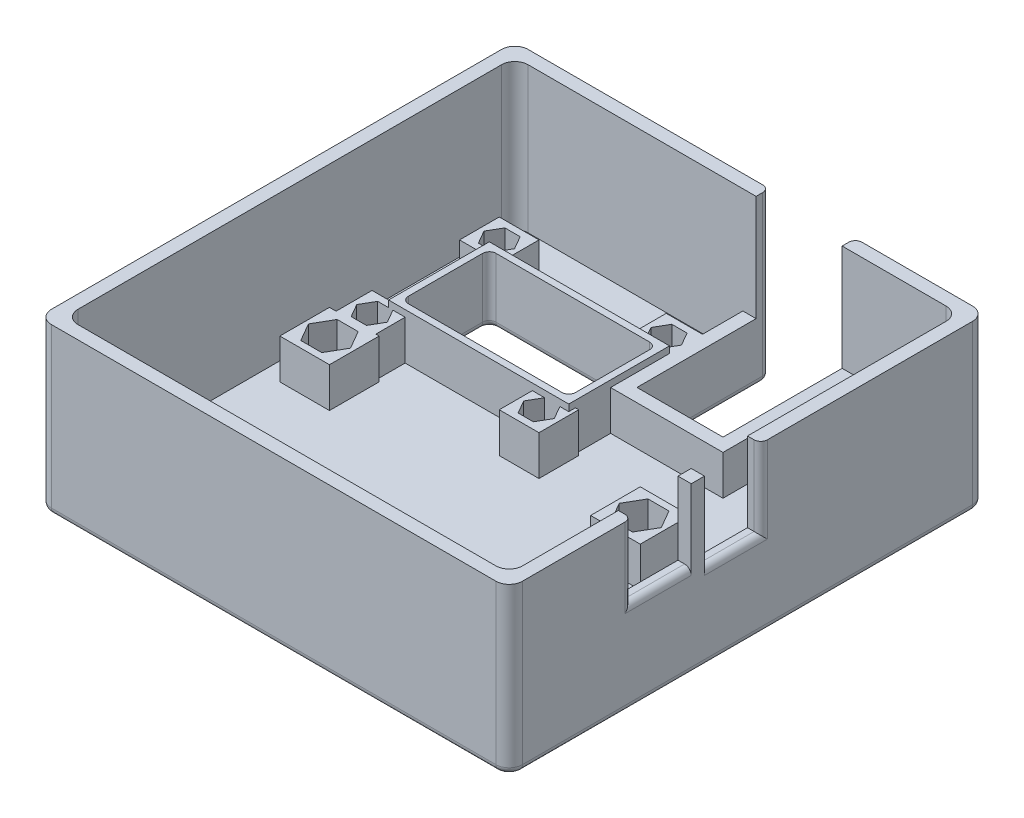
SolidWorks part; units mm, degrees
material "ABS"
ref_plane "Plano frontal" through (0, 0, 0) normal (0, 0, 1) x (1, 0, 0)
ref_plane "Plano superior" through (0, 0, 0) normal (0, 1, 0) x (1, 0, 0)
ref_plane "Plano direito" through (0, 0, 0) normal (1, 0, 0) x (0, 0, -1)
sketch "Esboço1" plane through (0, 0, 0) normal (0, 1, 0) x (1, 0, 0)
  line L1 (35.575, -36) -> (-35.575, -36)
  line L2 (35.575, -36) -> (35.575, 36)
  line L3 (35.575, 36) -> (-35.575, 36)
  line L4 (-35.575, -36) -> (-35.575, 36)
  line L5 (35.575, -36) -> (-35.575, 36) construction
  line L6 (35.575, 36) -> (-35.575, -36) construction
  point P0 (0, 0)
  dimension "D1" = 71.15
  dimension "D2" = 72
extrude "Ressalto-extrusão1" add sketch "Esboço1" along normal mid plane 3
sketch "Esboço2" plane through (0, 1.5, 0) normal (0, 1, 0) x (1, 0, 0)
  line L8 (-33.575, 34) -> (-33.575, -34)
  line L9 (-33.575, -34) -> (33.575, -34)
  line L10 (33.575, -34) -> (33.575, 34)
  line L11 (33.575, 34) -> (-33.575, 34)
  line L12 (-33.575, 34) -> (-33.575, -34)
  line L13 (-33.575, -34) -> (33.575, -34)
  line L14 (33.575, -34) -> (33.575, 34)
  line L15 (33.575, 34) -> (-33.575, 34)
  line L16 (-35.575, 36) -> (-35.575, -36)
  line L17 (-35.575, -36) -> (35.575, -36)
  line L18 (35.575, -36) -> (35.575, 36)
  line L19 (35.575, 36) -> (-35.575, 36)
  line L20 (-35.575, 36) -> (-35.575, -36)
  line L21 (-35.575, -36) -> (35.575, -36)
  line L22 (35.575, -36) -> (35.575, 36)
  line L23 (35.575, 36) -> (-35.575, 36)
  dimension "D1" = 2
  dimension "D2" = 0
extrude "Ressalto-extrusão2" add sketch "Esboço2" along normal blind 22
fillet "Filete1" radius 2 8 edges at (33.575, 12.5, -34) (35.575, 11, -36) (33.575, 12.5, 34) (35.575, 11, 36) (-33.575, 12.5, 34) (-35.575, 11, 36) (-35.575, 11, -36) (-33.575, 12.5, -34)
sketch "Esboço3" plane through (0, 0, -36) normal (0, 0, -1) x (-1, 0, 0)
  line L0 (-33.575, 23.5) -> (33.575, 23.5) construction
  line L1 (-15.875, 23.5) -> (-2.875, 23.5)
  line L2 (-15.875, 23.5) -> (-15.875, -1.5)
  line L3 (-15.875, -1.5) -> (-2.875, -1.5)
  line L4 (-2.875, 23.5) -> (-2.875, -1.5)
  line L6 (-33.575, -1.5) -> (33.575, -1.5) construction
  line L7 (-33.575, 23.5) -> (-33.575, -1.5) construction
  dimension "D1" = 17.7
  dimension "D2" = 13
extrude "Corte-extrusão1" cut sketch "Esboço3" against normal blind 20
sketch "Esboço4" plane through (0, 1.5, 0) normal (0, 1, 0) x (1, 0, 0)
  line L0 (17.875, 34) -> (17.875, 14)
  line L1 (17.875, 14) -> (0.875, 14)
  line L2 (0.875, 14) -> (0.875, 34)
  line L8 (15.875, 34) -> (15.875, 16)
  line L9 (15.875, 16) -> (2.875, 16)
  line L10 (2.875, 16) -> (2.875, 34)
  line L11 (2.875, 34) -> (-31.575, 34)
  line L12 (-33.575, 32) -> (-33.575, -32)
  line L13 (-31.575, -34) -> (31.575, -34)
  line L14 (33.575, -32) -> (33.575, 32)
  line L15 (31.575, 34) -> (15.875, 34)
  line L16 (15.875, 34) -> (15.875, 16)
  line L17 (15.875, 16) -> (2.875, 16)
  line L18 (2.875, 16) -> (2.875, 34)
  line L19 (2.875, 34) -> (0.875, 34)
  line L23 (17.875, 34) -> (15.875, 34)
  arc A4 (-31.575, 34) -> (-33.575, 32) centre (-31.575, 32) ccw
  arc A5 (-33.575, -32) -> (-31.575, -34) centre (-31.575, -32) ccw
  arc A6 (31.575, -34) -> (33.575, -32) centre (31.575, -32) ccw
  arc A7 (33.575, 32) -> (31.575, 34) centre (31.575, 32) ccw
  dimension "D1" = 0
  dimension "D2" = 2
extrude "Ressalto-extrusão3" add sketch "Esboço4" along normal blind 6
sketch "Esboço5" plane through (35.575, 0, 0) normal (1, 0, 0) x (0, 0, -1)
  line L0 (-34, 23.5) -> (34, 23.5) construction
  line L1 (-17.5, 23.5) -> (-8.5, 23.5)
  line L2 (-17.5, 23.5) -> (-17.5, 12.5)
  line L3 (-17.5, 12.5) -> (-8.5, 12.5)
  line L4 (-8.5, 23.5) -> (-8.5, 12.5)
  line L6 (-34, 23.5) -> (-34, -1.5) construction
  dimension "D1" = 16.5
  dimension "D2" = 9
  dimension "D3" = 11
extrude "Corte-extrusão2" cut sketch "Esboço5" against normal up to surface (2 mm away) and the other way through all up to face at (33.575, 12.5, 0)
sketch "Esboço6" plane through (35.575, 0, 0) normal (1, 0, 0) x (0, 0, -1)
  line L0 (-8.5, 23.5) -> (34, 23.5) construction
  line L1 (-6.5, 23.5) -> (2, 23.5)
  line L2 (-6.5, 23.5) -> (-6.5, 11.5)
  line L3 (-6.5, 11.5) -> (2, 11.5)
  line L4 (2, 23.5) -> (2, 11.5)
  line L5 (-34, 23.5) -> (-34, -1.5) construction
  dimension "D1" = 27.5
  dimension "D2" = 8.5
  dimension "D3" = 12
extrude "Corte-extrusão3" cut sketch "Esboço6" against normal up to surface (2 mm away) up to face at (33.575, 15.25, 6.5)
sketch "Esboço7" plane through (0, 1.5, 0) normal (0, 1, 0) x (1, 0, 0)
  line L0 (-31.575, -34) -> (31.575, -34) construction
  line L1 (-28.6627, -22.25) -> (-30.2504, -25)
  line L2 (-30.2504, -25) -> (-28.6627, -27.75)
  line L3 (-28.6627, -27.75) -> (-25.4873, -27.75)
  line L4 (-25.4873, -27.75) -> (-23.8996, -25)
  line L5 (-23.8996, -25) -> (-25.4873, -22.25)
  line L6 (-25.4873, -22.25) -> (-28.6627, -22.25)
  line L7 (-33.575, 32) -> (-33.575, -32) construction
  line L8 (-45.3985, -12.75) -> (20.9653, -12.75) construction
  line L9 (-23.325, -28.75) -> (-30.825, -28.75)
  line L10 (-23.325, -28.75) -> (-23.325, -21.25)
  line L11 (-23.325, -21.25) -> (-30.825, -21.25)
  line L12 (-30.825, -28.75) -> (-30.825, -21.25)
  line L13 (-23.325, -28.75) -> (-30.825, -21.25) construction
  line L14 (-23.325, -21.25) -> (-30.825, -28.75) construction
  line L15 (18.2873, -22.25) -> (16.6996, -25)
  line L16 (16.6996, -25) -> (18.2873, -27.75)
  line L17 (18.2873, -27.75) -> (21.4627, -27.75)
  line L18 (21.4627, -27.75) -> (23.0504, -25)
  line L19 (23.0504, -25) -> (21.4627, -22.25)
  line L20 (21.4627, -22.25) -> (18.2873, -22.25)
  line L21 (23.625, -28.75) -> (16.125, -28.75)
  line L22 (23.625, -28.75) -> (23.625, -21.25)
  line L23 (23.625, -21.25) -> (16.125, -21.25)
  line L24 (16.125, -28.75) -> (16.125, -21.25)
  line L25 (23.625, -28.75) -> (16.125, -21.25) construction
  line L26 (23.625, -21.25) -> (16.125, -28.75) construction
  line L27 (23.625, -4.25) -> (16.125, 3.25) construction
  line L28 (23.625, 3.25) -> (16.125, -4.25) construction
  line L29 (-23.325, -4.25) -> (-30.825, 3.25) construction
  line L30 (-23.325, 3.25) -> (-30.825, -4.25) construction
  line L31 (16.125, 3.25) -> (16.125, -4.25)
  line L32 (23.625, -4.25) -> (16.125, -4.25)
  line L33 (23.625, 3.25) -> (23.625, -4.25)
  line L34 (23.625, 3.25) -> (16.125, 3.25)
  line L35 (21.4627, -3.25) -> (18.2873, -3.25)
  line L36 (23.0504, -0.5) -> (21.4627, -3.25)
  line L37 (21.4627, 2.25) -> (23.0504, -0.5)
  line L38 (18.2873, 2.25) -> (21.4627, 2.25)
  line L39 (16.6996, -0.5) -> (18.2873, 2.25)
  line L40 (18.2873, -3.25) -> (16.6996, -0.5)
  line L41 (-30.825, 3.25) -> (-30.825, -4.25)
  line L42 (-23.325, -4.25) -> (-30.825, -4.25)
  line L43 (-23.325, 3.25) -> (-23.325, -4.25)
  line L44 (-23.325, 3.25) -> (-30.825, 3.25)
  line L45 (-25.4873, -3.25) -> (-28.6627, -3.25)
  line L46 (-23.8996, -0.5) -> (-25.4873, -3.25)
  line L47 (-25.4873, 2.25) -> (-23.8996, -0.5)
  line L48 (-28.6627, 2.25) -> (-25.4873, 2.25)
  line L49 (-30.2504, -0.5) -> (-28.6627, 2.25)
  line L50 (-28.6627, -3.25) -> (-30.2504, -0.5)
  circle A0 centre (-27.075, -25) radius 2.75 construction
  circle A1 centre (19.875, -25) radius 2.75 construction
  circle A2 centre (19.875, -0.5) radius 2.75 construction
  circle A3 centre (-27.075, -0.5) radius 2.75 construction
  dimension "D1" = 5.5
  dimension "D2" = 9
  dimension "D3" = 6.5
  dimension "D4" = 1
  dimension "D5" = 5.5
  dimension "D6" = 1
  dimension "D7" = 9
  dimension "D8" = 46.95
  dimension "D9" = 12.25
extrude "Ressalto-extrusão4" add sketch "Esboço7" along normal blind 6 contours L10 L9 L12 L11 | L1 L2 L3 L4 L5 L6 | L22 L21 L24 L23 | L15 L16 L17 L18 L19 L20 | L41 L42 L43 L44 | L45 L50 L49 L48 L47 L46 | L31 L32 L33 L34 | L35 L40 L39 L38 L37 L36
sketch "Esboço8" plane through (0, 1.5, 0) normal (0, 1, 0) x (1, 0, 0)
  line L0 (2.875, 34) -> (-31.575, 34) construction
  line L1 (-27.9797, 26.9) -> (-29.1344, 24.9)
  line L2 (-29.1344, 24.9) -> (-27.9797, 22.9)
  line L3 (-27.9797, 22.9) -> (-25.6703, 22.9)
  line L4 (-25.6703, 22.9) -> (-24.5156, 24.9)
  line L5 (-24.5156, 24.9) -> (-25.6703, 26.9)
  line L6 (-25.6703, 26.9) -> (-27.9797, 26.9)
  line L7 (-33.575, 32) -> (-33.575, -32) construction
  line L8 (-23.825, 21.9) -> (-29.825, 21.9)
  line L9 (-23.825, 21.9) -> (-23.825, 27.9)
  line L10 (-23.825, 27.9) -> (-29.825, 27.9)
  line L11 (-29.825, 21.9) -> (-29.825, 27.9)
  line L12 (-23.825, 21.9) -> (-29.825, 27.9) construction
  line L13 (-23.825, 27.9) -> (-29.825, 21.9) construction
  line L14 (0.875, 34) -> (-31.575, 34) construction
  line L16 (-2.7597, 26.9) -> (-3.9144, 24.9)
  line L17 (-3.9144, 24.9) -> (-2.7597, 22.9)
  line L18 (-2.7597, 22.9) -> (-0.4503, 22.9)
  line L19 (-0.4503, 22.9) -> (0.7044, 24.9)
  line L20 (0.7044, 24.9) -> (-0.4503, 26.9)
  line L21 (-0.4503, 26.9) -> (-2.7597, 26.9)
  line L22 (1.395, 21.9) -> (-4.605, 21.9)
  line L23 (1.395, 21.9) -> (1.395, 27.9)
  line L24 (1.395, 27.9) -> (-4.605, 27.9)
  line L25 (-4.605, 21.9) -> (-4.605, 27.9)
  line L26 (1.395, 21.9) -> (-4.605, 27.9) construction
  line L27 (1.395, 27.9) -> (-4.605, 21.9) construction
  line L28 (-2.7597, 7.68) -> (-3.9144, 5.68)
  line L29 (-3.9144, 5.68) -> (-2.7597, 3.68)
  line L30 (-2.7597, 3.68) -> (-0.4503, 3.68)
  line L31 (-0.4503, 3.68) -> (0.7044, 5.68)
  line L32 (0.7044, 5.68) -> (-0.4503, 7.68)
  line L33 (-0.4503, 7.68) -> (-2.7597, 7.68)
  line L34 (1.395, 2.68) -> (-4.605, 2.68)
  line L35 (1.395, 2.68) -> (1.395, 8.68)
  line L36 (1.395, 8.68) -> (-4.605, 8.68)
  line L37 (-4.605, 2.68) -> (-4.605, 8.68)
  line L38 (1.395, 2.68) -> (-4.605, 8.68) construction
  line L39 (1.395, 8.68) -> (-4.605, 2.68) construction
  line L40 (-27.9797, 7.68) -> (-29.1344, 5.68)
  line L41 (-29.1344, 5.68) -> (-27.9797, 3.68)
  line L42 (-27.9797, 3.68) -> (-25.6703, 3.68)
  line L43 (-25.6703, 3.68) -> (-24.5156, 5.68)
  line L44 (-24.5156, 5.68) -> (-25.6703, 7.68)
  line L45 (-25.6703, 7.68) -> (-27.9797, 7.68)
  line L46 (-23.825, 2.68) -> (-29.825, 2.68)
  line L47 (-23.825, 2.68) -> (-23.825, 8.68)
  line L48 (-23.825, 8.68) -> (-29.825, 8.68)
  line L49 (-29.825, 2.68) -> (-29.825, 8.68)
  line L50 (-23.825, 2.68) -> (-29.825, 8.68) construction
  line L51 (-23.825, 8.68) -> (-29.825, 2.68) construction
  circle A0 centre (-26.825, 24.9) radius 2 construction
  circle A1 centre (-1.605, 24.9) radius 2 construction
  circle A2 centre (-1.605, 5.68) radius 2 construction
  circle A3 centre (-26.825, 5.68) radius 2 construction
  dimension "D1" = 4
  dimension "D2" = 1
  dimension "D3" = 6.75
  dimension "D4" = 9.1
  dimension "D5" = 4
  dimension "D6" = 1
  dimension "D7" = 25.22
  dimension "D8" = 9.1
  dimension "D9" = 4
  dimension "D10" = 1
  dimension "D11" = 19.22
  dimension "D12" = 4
  dimension "D13" = 1
extrude "Ressalto-extrusão5" add sketch "Esboço8" along normal blind 6
sketch "Esboço9" plane through (0, 1.5, 0) normal (0, 1, 0) x (1, 0, 0)
  line L0 (-23.825, 21.9) -> (-4.605, 21.9)
  line L10 (-23.825, 21.9) -> (-25.325, 21.9)
  line L11 (-4.605, 8.68) -> (-23.825, 8.68)
  line L12 (-0.105, 21.9) -> (-0.105, 8.68)
  line L13 (-4.605, 21.9) -> (0.875, 21.9) construction
  line L14 (1.395, 8.68) -> (-4.605, 8.68) construction
  line L18 (-23.825, 8.68) -> (-25.325, 8.68)
  line L19 (-0.105, 8.68) -> (-4.605, 8.68)
  line L20 (-4.605, 21.9) -> (-0.105, 21.9)
  line L31 (-25.325, 21.9) -> (-25.325, 8.68)
  line L32 (-23.825, 22.9) -> (-4.605, 22.9)
  line L33 (-4.605, 22.9) -> (0.895, 22.9)
  line L34 (0.895, 22.9) -> (0.895, 7.68)
  line L35 (0.895, 7.68) -> (-4.605, 7.68)
  line L36 (-4.605, 7.68) -> (-23.825, 7.68)
  line L37 (-23.825, 7.68) -> (-26.325, 7.68)
  line L38 (-26.325, 22.9) -> (-26.325, 7.68)
  line L39 (-23.825, 22.9) -> (-26.325, 22.9)
  line L40 (-4.605, 27.9) -> (-4.605, 21.9) construction
  dimension "D1" = 4.5
  dimension "D2" = 4.5
  dimension "D3" = 1
extrude "Ressalto-extrusão6" add sketch "Esboço9" along normal blind 7
sketch "Esboço10" plane through (0, 1.5, 0) normal (0, 1, 0) x (1, 0, 0)
  line L4 (-25.325, 8.68) -> (-0.105, 8.68)
  line L6 (-25.325, 8.68) -> (-0.105, 8.68)
  line L12 (-0.105, 8.68) -> (-0.105, 21.9)
  line L13 (-0.105, 8.68) -> (-0.105, 21.9)
  line L14 (-0.105, 21.9) -> (-25.325, 21.9)
  line L16 (-0.105, 21.9) -> (-25.325, 21.9)
  line L18 (-25.325, 21.9) -> (-25.325, 8.68)
  line L20 (-25.325, 21.9) -> (-25.325, 8.68)
  dimension "D1" = 0
extrude "Corte-extrusão4" cut sketch "Esboço10" against normal up to surface (3 mm away) up to face at (3.125, -1.5, -8.6667)
fillet "Filete3" radius 1 8 edges at (-0.105, -1.5, -15.29) (-12.715, -1.5, -21.9) (-12.715, -1.5, -8.68) (-25.325, -1.5, -15.29) (-25.325, 3.5, -21.9) (-25.325, 3.5, -8.68) (-0.105, 3.5, -8.68) (-0.105, 3.5, -21.9)
fillet "Filete4" radius 1 18 edges at (2.875, -1.5, -26) (-15.35, -1.5, -36) (-34.9892, -1.5, -35.4142) (-35.575, -1.5, 0) (-34.9892, -1.5, 35.4142) (0, -1.5, 36) (34.9892, -1.5, 35.4142) (35.575, -1.5, 0) (34.9892, -1.5, -35.4142) (24.725, -1.5, -36) (15.875, -1.5, -26) (9.375, -1.5, -16) (35.575, 18, 17.5) (35.575, 12.5, 13) (35.575, 11.5, 2.25) (35.575, 17.5, -2) (15.875, 11, -36) (2.875, 11, -36)
